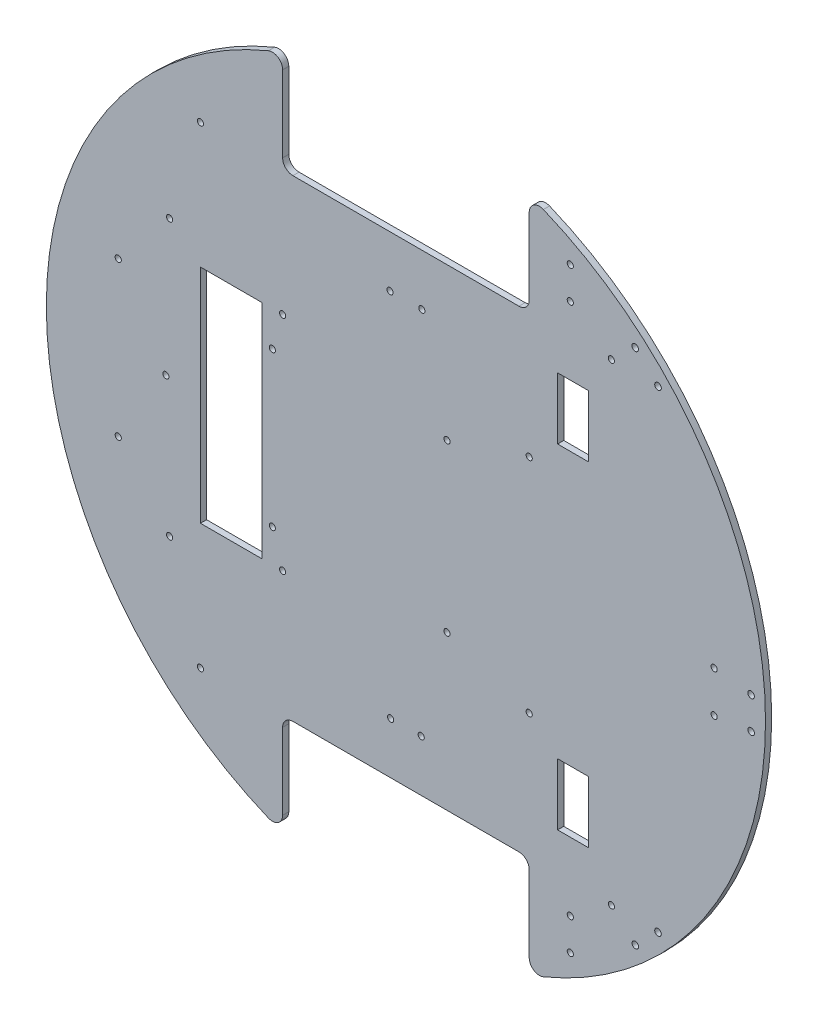
SolidWorks part; units mm, degrees
material "ｱｸﾘﾙ (中-上級の耐衝撃性)"
ref_plane "正面" through (0, 0, 0) normal (0, 0, 1) x (1, 0, 0)
ref_plane "平面" through (0, 0, 0) normal (0, 1, 0) x (1, 0, 0)
ref_plane "右側面" through (0, 0, 0) normal (1, 0, 0) x (0, 0, -1)
sketch "ｽｹｯﾁ1" plane through (0, 0, 0) normal (0, 0, 1) x (1, 0, 0)
  circle A0 centre (0, 0) radius 175
  dimension "D1" = 350
extrude "ﾎﾞｽ - 押し出し1" add sketch "ｽｹｯﾁ1" along normal blind 3
sketch "ｽｹｯﾁ2" plane through (0, 0, 3) normal (0, 0, 1) x (1, 0, 0)
  line L0 (0, 0) -> (175, 0)
  line L1 (0, 0) -> (-175, 0)
  line L2 (0, 0) -> (0, 115)
  line L3 (0, 0) -> (0, -115)
  line L4 (0, 115) -> (60, 115)
  line L5 (0, 115) -> (0, 175)
  line L6 (0, 175) -> (60, 175)
  line L7 (60, 115) -> (60, 175)
  line L8 (0, 115) -> (-60, 115)
  line L9 (0, 115) -> (0, 175)
  line L10 (0, 175) -> (-60, 175)
  line L11 (-60, 115) -> (-60, 175)
  line L13 (0, -115) -> (60, -115)
  line L14 (0, -115) -> (0, -175)
  line L15 (0, -175) -> (60, -175)
  line L16 (60, -115) -> (60, -175)
  line L17 (0, -115) -> (-60, -115)
  line L18 (0, -115) -> (0, -175)
  line L19 (0, -175) -> (-60, -175)
  line L20 (-60, -115) -> (-60, -175)
  circle A0 centre (0, 0) radius 175 construction
  circle M1 centre (0, 0) radius 175
  dimension "D1" = 115
  dimension "D2" = 60
  dimension "D3" = 60
  dimension "D4" = 60
  dimension "D5" = 115
  dimension "D6" = 60
extrude "ｶｯﾄ - 押し出し1" cut sketch "ｽｹｯﾁ2" against normal blind 3 contours L11 L8 L5 M1 | L4 L7 L5 M1 | L17 L20 L14 M1 | L16 L13 L14 M1
fillet "ﾌｨﾚｯﾄ1" radius 5 1 edges at (-60, 164.3928, 1.5)
fillet "ﾌｨﾚｯﾄ2" radius 5 3 edges at (60, 115, 1.5) (60, 164.3928, 1.5) (-60, 115, 1.5)
fillet "ﾌｨﾚｯﾄ3" radius 5 4 edges at (-60, -164.3928, 1.5) (-60, -115, 1.5) (60, -164.3928, 1.5) (60, -115, 1.5)
sketch "ｽｹｯﾁ5" plane through (0, 0, 3) normal (0, 0, 1) x (1, 0, 0)
  line L0 (0, 115) -> (-100, 115)
  line L1 (55, 115) -> (-55, 115) construction
  line L2 (0, 115) -> (100, 115)
  line L3 (0, -115) -> (100, -115)
  line L4 (55, -115) -> (-55, -115) construction
  line L5 (100, -115) -> (-100, -115)
  circle A0 centre (-100, -115) radius 1.5
  circle A1 centre (100, -115) radius 1.5
  circle A2 centre (100, 115) radius 1.5
  circle A3 centre (-100, 115) radius 1.5
  dimension "D3" = 3
  dimension "D4" = 3
  dimension "D5" = 3
  dimension "D6" = 3
  dimension "D1" = 100
  dimension "D2" = 100
extrude "ｶｯﾄ - 押し出し4" cut sketch "ｽｹｯﾁ5" against normal blind 3 contours A1 | A0 | A3 | A2
sketch "ｽｹｯﾁ6" plane through (0, 0, 3) normal (0, 0, 1) x (1, 0, 0)
  line L1 (-60, 54) -> (60, 54)
  line L2 (-60, 54) -> (-60, -54)
  line L3 (-60, -54) -> (60, -54)
  line L4 (60, 54) -> (60, -54)
  line L5 (-60, 54) -> (60, -54) construction
  line L6 (-60, -54) -> (60, 54) construction
  circle A0 centre (-60, 54) radius 1.5
  circle A1 centre (60, 54) radius 1.5
  circle A2 centre (-60, -54) radius 1.5
  circle A3 centre (60, -54) radius 1.5
  point P0 (0, 0)
  dimension "D3" = 3
  dimension "D4" = 3
  dimension "D5" = 3
  dimension "D6" = 3
  dimension "D1" = 120
  dimension "D2" = 108
extrude "ｶｯﾄ - 押し出し5" cut sketch "ｽｹｯﾁ6" against normal blind 3 contours A2 | A0 | A1 | A3
sketch "ｽｹｯﾁ7" plane through (0, 0, 3) normal (0, 0, 1) x (1, 0, 0)
  line L0 (-60, -54) -> (-70, -54)
  line L2 (-70, -54) -> (-100, -54)
  line L3 (-70, -54) -> (-70, 54)
  line L4 (-70, 54) -> (-100, 54)
  line L5 (-100, -54) -> (-100, 54)
  dimension "D1" = 10
  dimension "D2" = 108
  dimension "D3" = 30
extrude "ｶｯﾄ - 押し出し6" cut sketch "ｽｹｯﾁ7" against normal blind 3 contours L5 L2 L3 L4
sketch "ｽｹｯﾁ8" plane through (0, 0, 3) normal (0, 0, 1) x (1, 0, 0)
  line L0 (-100, 0) -> (-115, 0)
  line L1 (-100, -54) -> (-100, 54) construction
  line L2 (-115, 0) -> (-115, 67)
  line L3 (-115, 0) -> (-115, -67)
  circle A0 centre (-115, -67) radius 1.5
  circle A1 centre (-116.8225, 0) radius 1.5
  circle A2 centre (-115, 67) radius 1.5
  dimension "D4" = 3
  dimension "D5" = 3
  dimension "D6" = 3
  dimension "D1" = 15
  dimension "D2" = 67
  dimension "D3" = 67
extrude "ｶｯﾄ - 押し出し7" cut sketch "ｽｹｯﾁ8" against normal blind 3 contours A2 | A1 | A0
sketch "ｽｹｯﾁ9" plane through (0, 0, 3) normal (0, 0, 1) x (1, 0, 0)
  line L0 (-70, 0) -> (-65, 0)
  line L1 (-70, -54) -> (-70, 54) construction
  line L2 (-65, 0) -> (-65, 37)
  line L3 (-65, 37) -> (-64.7716, 37.1905)
  line L4 (-65, 0) -> (-65, -38)
  line L5 (-65, 0) -> (20, 0)
  line L6 (20, 0) -> (20, 41)
  line L7 (20, 0) -> (20, -40)
  circle A0 centre (-65, 37) radius 1.5
  circle A1 centre (20, 41) radius 1.5
  circle A2 centre (-65, -38) radius 1.5
  circle A3 centre (20, -40) radius 1.5
  dimension "D7" = 3
  dimension "D8" = 3
  dimension "D9" = 3
  dimension "D10" = 3
  dimension "D1" = 5
  dimension "D2" = 37
  dimension "D3" = 38
  dimension "D4" = 85
  dimension "D5" = 41
  dimension "D6" = 40
extrude "ｶｯﾄ - 押し出し8" cut sketch "ｽｹｯﾁ9" against normal blind 10 contours A0 | A2 | A1 | A3
sketch "ｽｹｯﾁ10" plane through (0, 0, 3) normal (0, 0, 1) x (1, 0, 0)
  line L0 (0, 0) -> (152.2366, 0)
  line L1 (0, 0) -> (66.9742, 68.8711)
  line L2 (0, 0) -> (76.2283, -78.3873)
  line L3 (175, 0) -> (168, 0)
  line L4 (-175, 0) -> (-168, 0)
  line L5 (66.9742, 68.8711) -> (117.1237, 120.441)
  line L6 (76.2283, -78.3873) -> (117.1237, -120.441)
  line L7 (117.1237, -120.441) -> (122.6798, -115.038)
  line L8 (117.1237, -120.441) -> (111.6437, -125.9211)
  line L9 (168, 0) -> (168, 7.75)
  line L10 (168, 0) -> (168, -7.75)
  line L11 (117.1237, 120.441) -> (111.5677, 125.844)
  line L12 (117.1237, 120.441) -> (122.6798, 115.038)
  arc A0 (66.9118, -161.7029) -> (66.9118, 161.7029) centre (0, 0) ccw construction
  arc A1 (-66.9118, 161.7029) -> (-66.9118, -161.7029) centre (0, 0) ccw construction
  circle A2 centre (0, 0) radius 168
  circle A3 centre (111.6437, -125.9211) radius 1.6
  circle A4 centre (122.6798, -115.038) radius 1.6
  circle A5 centre (168, 7.75) radius 1.6
  circle A6 centre (168, -7.75) radius 1.6
  circle A7 centre (111.5677, 125.844) radius 1.6
  circle A8 centre (122.6798, 115.038) radius 1.6
  dimension "D7" = 3.2
  dimension "D8" = 3.2
  dimension "D11" = 3.2
  dimension "D12" = 3.2
  dimension "D15" = 3.2
  dimension "D16" = 3.2
  dimension "D1" = 45.8
  dimension "D2" = 45.8
  dimension "D3" = 7
  dimension "D4" = 7
  dimension "D5" = 7.75
  dimension "D6" = 7.75
  dimension "D9" = 7.75
  dimension "D10" = 7.75
  dimension "D13" = 7.75
  dimension "D14" = 7.75
extrude "ｶｯﾄ - 押し出し9" cut sketch "ｽｹｯﾁ10" against normal blind 10 contours A3 | A4 | A6 | A5 | A7 | A8
sketch "ｽｹｯﾁ11" plane through (0, 0, 3) normal (0, 0, 1) x (1, 0, 0)
  line L0 (0, 0) -> (115, 0)
  line L1 (0, 0) -> (81.3173, 81.3173)
  line L2 (0, 0) -> (81.3173, -81.3173)
  line L4 (73.8173, 96.3173) -> (88.8173, 96.3173)
  line L5 (73.8173, 96.3173) -> (73.8173, 66.3173)
  line L6 (73.8173, 66.3173) -> (88.8173, 66.3173)
  line L7 (88.8173, 96.3173) -> (88.8173, 66.3173)
  line L8 (73.8173, 96.3173) -> (88.8173, 66.3173) construction
  line L9 (73.8173, 66.3173) -> (88.8173, 96.3173) construction
  line L10 (73.8173, -66.3173) -> (88.8173, -66.3173)
  line L11 (73.8173, -66.3173) -> (73.8173, -96.3173)
  line L12 (73.8173, -96.3173) -> (88.8173, -96.3173)
  line L13 (88.8173, -66.3173) -> (88.8173, -96.3173)
  line L14 (73.8173, -66.3173) -> (88.8173, -96.3173) construction
  line L15 (73.8173, -96.3173) -> (88.8173, -66.3173) construction
  circle A0 centre (0, 0) radius 115
  dimension "D1" = 230
  dimension "D2" = 45
  dimension "D3" = 45
  dimension "D4" = 30
  dimension "D5" = 15
  dimension "D6" = 15
  dimension "D7" = 30
extrude "ｶｯﾄ - 押し出し10" cut sketch "ｽｹｯﾁ11" against normal blind 10 contours L7 L6 L5 L4 | L13 L12 L11 L10
sketch "ｽｹｯﾁ17" plane through (0, 0, 3) normal (0, 0, 1) x (1, 0, 0)
  circle A0 centre (-7.75, 90) radius 1.5
  circle A1 centre (7.75, 90) radius 1.5
  circle A2 centre (7.45, -90) radius 1.5
  circle A3 centre (-7.45, -90) radius 1.5
  dimension "D1" = 3
  dimension "D5" = 90
  dimension "D7" = 7.75
  dimension "D8" = 7.75
extrude "ｶｯﾄ - 押し出し12" cut sketch "ｽｹｯﾁ17" against normal through all
sketch "ｽｹｯﾁ29" plane through (0, 0, 3) normal (0, 0, 1) x (1, 0, 0)
  circle A0 centre (80, 145) radius 1.5
  circle A1 centre (80, 129.5) radius 1.5
  dimension "D1" = 3
  dimension "D4" = 3
  dimension "D3" = 145
  dimension "D5" = 129.5
  dimension "D6" = 80
extrude "超音波(左)" cut sketch "ｽｹｯﾁ29" against normal through all
sketch "ｽｹｯﾁ30" plane through (0, 0, 3) normal (0, 0, 1) x (1, 0, 0)
  circle A0 centre (80, -129.5) radius 1.5
  circle A1 centre (80, -145) radius 1.5
  dimension "D1" = 3
  dimension "D4" = 3
  dimension "D2" = 80
  dimension "D3" = 129.5
  dimension "D5" = 145
extrude "超音波(右)" cut sketch "ｽｹｯﾁ30" against normal through all
sketch "ｽｹｯﾁ31" plane through (0, 0, 3) normal (0, 0, 1) x (1, 0, 0)
  circle A0 centre (-140, 37.5) radius 1.5
  circle A1 centre (-140, -37.5) radius 1.5
  dimension "D1" = 3
  dimension "D4" = 3
  dimension "D2" = 140
  dimension "D3" = 37.5
  dimension "D5" = 37.5
  dimension "D6" = 140
extrude "電源ボード" cut sketch "ｽｹｯﾁ31" against normal through all
sketch "ｽｹｯﾁ32" plane through (0, 0, 3) normal (0, 0, 1) x (1, 0, 0)
  circle A0 centre (150, 10) radius 1.5
  circle A1 centre (150, -10) radius 1.5
  dimension "D1" = 3
  dimension "D2" = 10
  dimension "D4" = 3
  dimension "D5" = 10
  dimension "D3" = 150
extrude "WEBカメラ" cut sketch "ｽｹｯﾁ32" against normal through all
